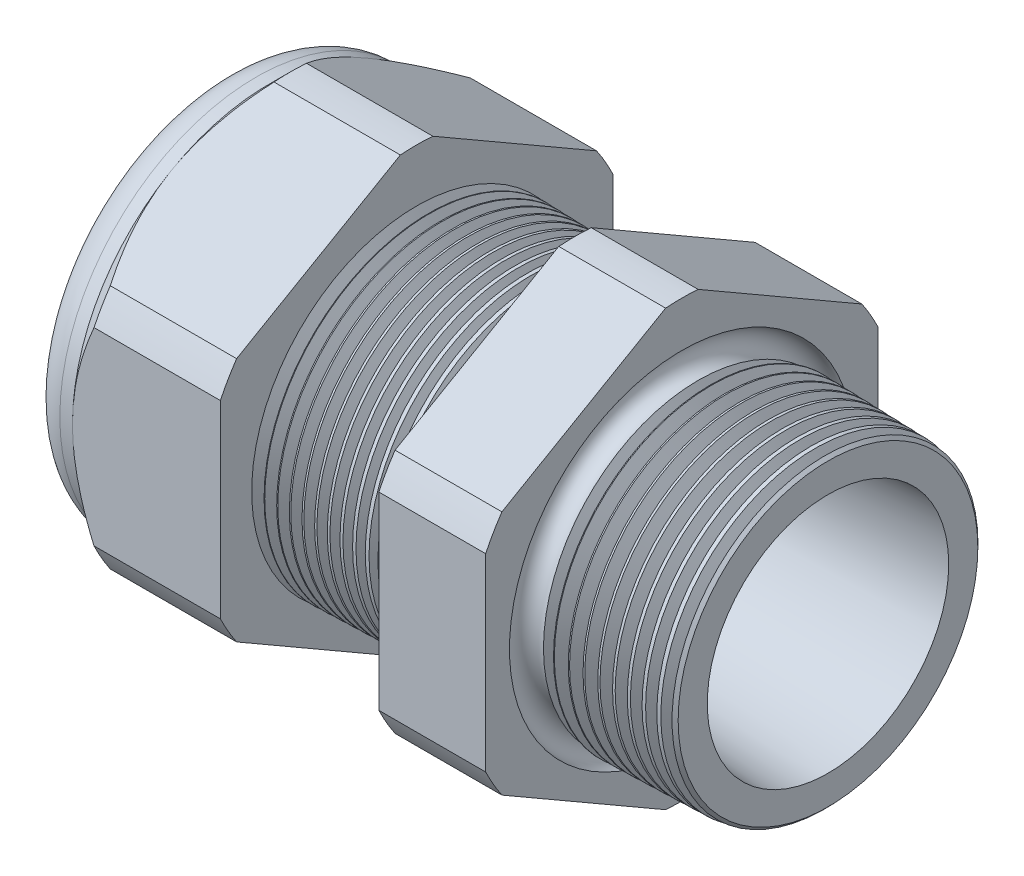
SolidWorks part; units mm, degrees
ref_plane "Front Plane" through (0, 0, 0) normal (0, 0, 1) x (1, 0, 0)
ref_plane "Top Plane" through (0, 0, 0) normal (0, 1, 0) x (1, 0, 0)
ref_plane "Right Plane" through (0, 0, 0) normal (1, 0, 0) x (0, 0, -1)
sketch "Sketch10" plane through (0, 0, 0) normal (0, 0, 1) x (1, 0, 0)
  line L0 (0, 0) -> (-115.3565, 0) construction
  line L1 (-35.814, 5.969) -> (-24.014, 5.969)
  line L2 (1.016, 7.3456) -> (1.016, 9.3776)
  line L3 (-7.874, 9.6104) -> (1.016, 9.3776)
  line L4 (-7.874, 23.876) -> (-7.874, 9.6104)
  line L5 (-7.874, 23.876) -> (-14.374, 23.876)
  line L6 (-14.374, 23.876) -> (-14.374, 9.7806)
  line L7 (-24.014, 10.033) -> (-14.374, 9.7806)
  line L8 (-24.014, 10.033) -> (-24.014, 23.876)
  line L9 (-24.014, 23.876) -> (-33.014, 23.876)
  line L10 (-33.014, 23.876) -> (-33.014, 11.938)
  line L11 (-33.014, 11.938) -> (-35.814, 11.938)
  line L12 (-35.814, 11.938) -> (-35.814, 5.969)
  line L13 (-24.014, 5.969) -> (1.016, 7.3456)
  dimension "D1" = 36.83
  dimension "D2" = 11.938
  dimension "D3" = 1.5
  dimension "D4" = 2.032
  dimension "A" = 20.066
  dimension "D6" = 23.876
  dimension "D8" = 47.752
  dimension "D9" = 2.8
  dimension "D10" = 9
  dimension "D11" = 6.5
  dimension "D" = 8.89
revolve "Revolve2" add sketch "Sketch10" angle 360 about L0
sketch "Sketch12" plane through (-33.014, 0, 0) normal (-1, 0, 0) x (0, 0, 1)
  line L1 (-0.9882, 13.2143) -> (-10.9498, 7.4629)
  line L2 (-11.938, 5.7513) -> (-11.938, -5.7513)
  line L3 (-10.9498, -7.4629) -> (-0.9882, -13.2143)
  line L4 (0.9882, -13.2143) -> (10.9498, -7.4629)
  line L5 (11.938, -5.7513) -> (11.938, 5.7513)
  line L6 (10.9498, 7.4629) -> (0.9882, 13.2143)
  circle A0 centre (0, 0) radius 11.938 construction
  arc A1 (0.9882, 13.2143) -> (-0.9882, 13.2143) centre (0, 0) ccw
  arc A2 (-10.9498, 7.4629) -> (-11.938, 5.7513) centre (0, 0) ccw
  arc A3 (-11.938, -5.7513) -> (-10.9498, -7.4629) centre (0, 0) ccw
  arc A4 (-0.9882, -13.2143) -> (0.9882, -13.2143) centre (0, 0) ccw
  arc A5 (10.9498, -7.4629) -> (11.938, -5.7513) centre (0, 0) ccw
  arc A6 (11.938, 5.7513) -> (10.9498, 7.4629) centre (0, 0) ccw
  dimension "D2" = 26.5024
  dimension "D1" = 23.876
extrude "Cut-Extrude2" cut sketch "Sketch12" against normal through all flip side to cut
fillet "Fillet4" radius 2.032 1 edges at (-35.814, 0, -11.938)
sketch "Sketch19" plane through (-33.014, 0, 0) normal (-1, 0, 0) x (0, 0, 1)
  line L0 (11.938, 0) -> (11.938, 5.7513) construction
  circle A0 centre (0, 0) radius 11.938
extrude "Cut-Extrude3" cut sketch "Sketch19" against normal blind 2 draft 45 flip side to cut
chamfer "Chamfer1" distance 0.254 angle 45 1 edges at (1.016, 0, -9.3776)
sketch "Sketch21" plane through (-35.814, 0, 0) normal (-1, 0, 0) x (0, 0, 1)
  circle A0 centre (0, 0) radius 5.969
  circle A2 centre (0, 0) radius 5.969 construction
extrude "plug" add sketch "Sketch21" against normal blind 6.35 separate body
sketch "Sketch22" plane through (-35.814, 0, 0) normal (-1, 0, 0) x (0, 0, 1)
  circle A0 centre (0, 0) radius 5.715
  circle A1 centre (0, 0) radius 5.969 construction
  dimension "D1" = 0.254
extrude "Cut-Extrude4" cut sketch "Sketch22" against normal blind 0.508
sketch "Sketch27" plane through (-35.306, 0, 0) normal (-1, 0, 0) x (0, 0, 1)
  line L0 (-4.3624, 0) -> (4.3624, 0) construction
  circle A0 centre (-3.6749, 0) radius 2.032
  circle A1 centre (0, 0) radius 5.715 construction
  dimension "D1" = 0.0081
  dimension "holedia" = 4.064
extrude "plugholes" cut sketch "Sketch27" against normal through all
pattern_circular "CirPattern1" count 4 over 360 about axis through (0, 0, 0) along (1, 0, 0) of "plugholes"
sketch "Sketch28" [suppressed] plane through (-29.464, 0, 0) normal (-1, 0, 0) x (0, 0, 1)
  circle A0 centre (0, 0) radius 0.762
  dimension "midholedia" = 4.064
extrude "midhole" [suppressed] cut sketch "Sketch28" against normal through all
sketch "Sketch29" plane through (0, 0, 0) normal (0, 0, 1) x (1, 0, 0)
  line L0 (-24.014, 10.033) -> (-23.281, 10.0138)
  line L1 (-14.374, 9.7806) -> (-24.014, 10.033) construction
  line L2 (-23.281, 10.0138) -> (-23.6641, 9.3886)
  line L3 (-23.6641, 9.3886) -> (-24.014, 10.033)
  dimension "D1" = 60
  dimension "D2" = 60
  dimension "D3" = 0.635
revolve "Cut-Revolve1" cut sketch "Sketch29" angle 360 about axis through (0, 0, 0) along (-1, 0, 0)
pattern_linear "LPattern1" count 13 spacing 0.762 along (1, 0, 0) of "Cut-Revolve1"
sketch "Sketch30" plane through (0, 0, 0) normal (0, 0, 1) x (1, 0, 0)
  line L0 (-7.874, 9.6104) -> (-6.9944, 9.5873)
  line L1 (-7.874, 13.2143) -> (-7.874, 7.4629) construction
  line L2 (0.7621, 9.3842) -> (-7.874, 9.6104) construction
  line L3 (-6.9944, 9.5873) -> (-7.4542, 8.8371)
  line L4 (-7.4542, 8.8371) -> (-7.874, 9.6104)
  dimension "D1" = 60
  dimension "D2" = 60
  dimension "D3" = 0.762
revolve "Cut-Revolve2" cut sketch "Sketch30" angle 360 about axis through (0, 0, 0) along (-1, 0, 0)
pattern_linear "LPattern2" count 10 spacing 0.889 along (1, 0, 0) of "Cut-Revolve2"
sketch "Sketch31" [suppressed] plane through (-38.354, 0, 0) normal (-1, 0, 0) x (0, 0, 1)
  line L0 (-1.905, 1.905) -> (1.905, 1.905)
  line L1 (-1.905, -1.905) -> (1.905, -1.905)
  circle A0 centre (0, 0) radius 1.905 construction
  arc A1 (-1.905, 1.905) -> (-1.905, -1.905) centre (-1.905, 0) ccw
  arc A2 (1.905, 1.905) -> (1.905, -1.905) centre (1.905, 0) cw
extrude "Cut-Extrude5" [suppressed] cut sketch "Sketch31" against normal through all
sketch "Sketch32" plane through (0, 0, 0) normal (0, 0, 1) x (1, 0, 0)
  line L0 (-7.874, 13.2143) -> (-7.874, 7.4629) construction
  circle A0 centre (-7.747, 9.6104) radius 0.889
  dimension "D2" = 1.778
  dimension "D1" = 0.127
revolve "Cut-Revolve3" cut sketch "Sketch32" angle 360 about axis through (0, 0, 0) along (-1, 0, 0)
